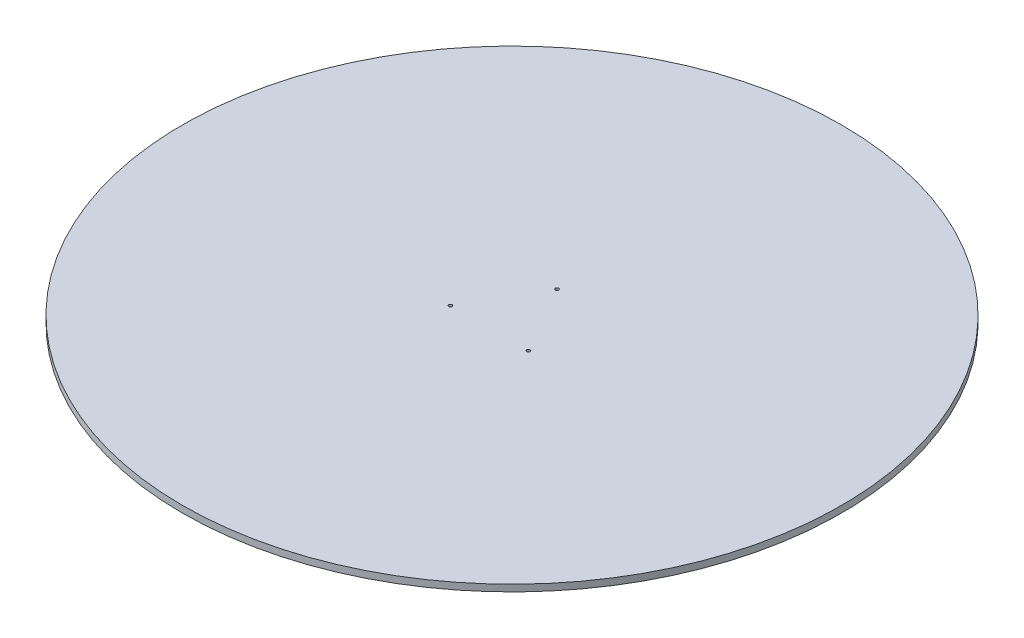
SolidWorks part; units mm, degrees
material "7075-T6 (SN)"
ref_plane "Front Plane" through (0, 0, 0) normal (0, 0, 1) x (1, 0, 0)
ref_plane "Top Plane" through (0, 0, 0) normal (0, 1, 0) x (1, 0, 0)
ref_plane "Right Plane" through (0, 0, 0) normal (1, 0, 0) x (0, 0, -1)
sketch "Sketch1" plane through (0, 0, 0) normal (0, 1, 0) x (1, 0, 0)
  circle A0 centre (0, 0) radius 1250
  circle A1 centre (0, 170.8836) radius 6.35
  circle A2 centre (147.9896, -85.4418) radius 6.35
  circle A3 centre (-147.9896, -85.4418) radius 6.35
  point P11 (0, 0)
  dimension "D1" = 2500
  dimension "D3" = 12.7
  dimension "D2" = 3
extrude "Boss-Extrude1" add sketch "Sketch1" along normal blind 25.4 contours A0 A3 A2 A1
